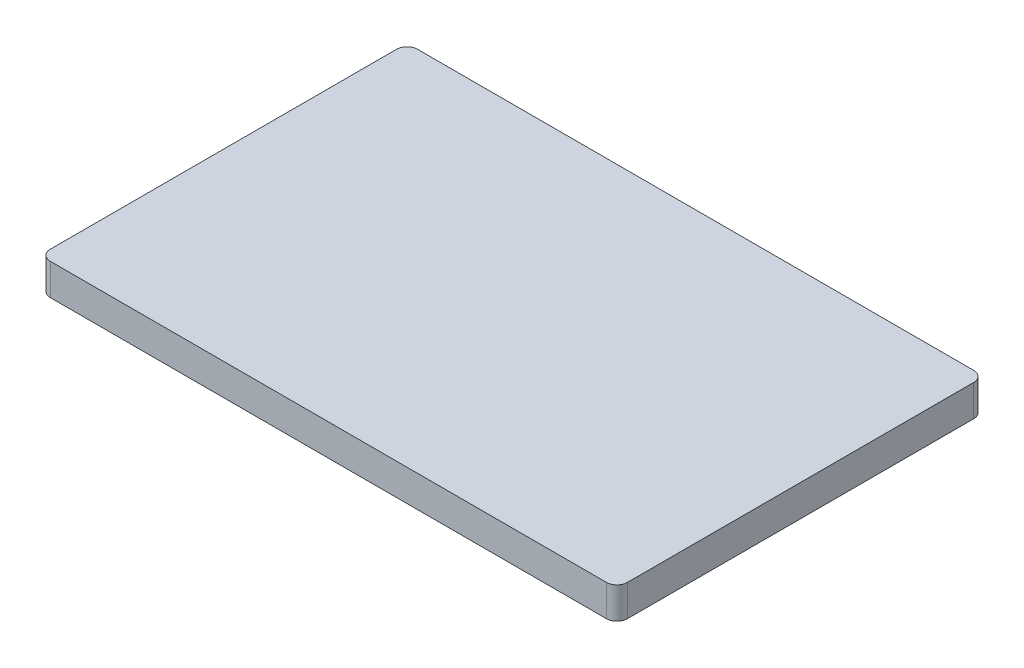
SolidWorks part; units mm, degrees
material "天然橡胶"
ref_plane "前视基准面" through (0, 0, 0) normal (0, 0, 1) x (1, 0, 0)
ref_plane "上视基准面" through (0, 0, 0) normal (0, 1, 0) x (1, 0, 0)
ref_plane "右视基准面" through (0, 0, 0) normal (1, 0, 0) x (0, 0, -1)
sketch "草图1" plane through (0, 0, 0) normal (0, 1, 0) x (1, 0, 0)
  line L1 (26.5, -17.5) -> (-26.5, -17.5)
  line L2 (27.5, -16.5) -> (27.5, 16.5)
  line L3 (26.5, 17.5) -> (-26.5, 17.5)
  line L4 (-27.5, -16.5) -> (-27.5, 16.5)
  line L5 (27.5, -17.5) -> (-27.5, 17.5) construction
  line L6 (27.5, 17.5) -> (-27.5, -17.5) construction
  arc A0 (26.5, -17.5) -> (27.5, -16.5) centre (26.5, -16.5) ccw
  arc A1 (27.5, 16.5) -> (26.5, 17.5) centre (26.5, 16.5) ccw
  arc A2 (-26.5, 17.5) -> (-27.5, 16.5) centre (-26.5, 16.5) ccw
  arc A3 (-26.5, -17.5) -> (-27.5, -16.5) centre (-26.5, -16.5) cw
  point P0 (0, 0)
  dimension "D3" = 1
  dimension "D1" = 55
  dimension "D2" = 35
extrude "凸台-拉伸1" add sketch "草图1" along normal blind 3
